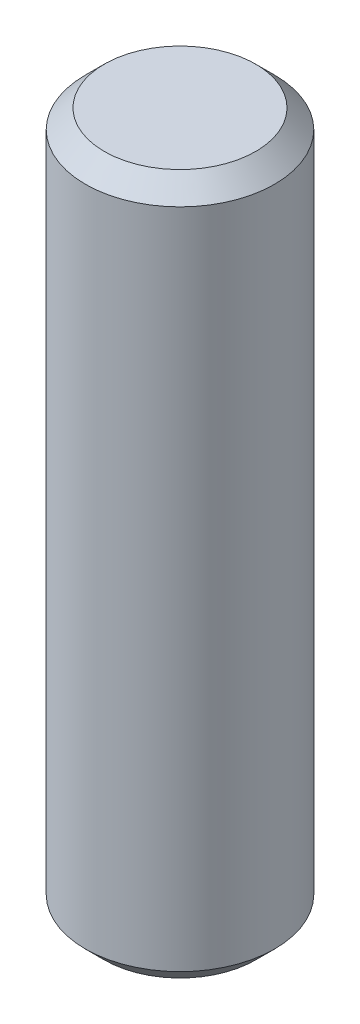
SolidWorks part; units mm, degrees
ref_plane "Front Plane" through (0, 0, 0) normal (0, 0, 1) x (1, 0, 0)
ref_plane "Top Plane" through (0, 0, 0) normal (0, 1, 0) x (1, 0, 0)
ref_plane "Right Plane" through (0, 0, 0) normal (1, 0, 0) x (0, 0, -1)
sketch "Sketch1" plane through (0, 0, 0) normal (0, 1, 0) x (1, 0, 0)
  circle A0 centre (0, 0) radius 10
  dimension "D1" = 20
extrude "Boss-Extrude1" add sketch "Sketch1" along normal mid plane 74
chamfer "Chamfer1" distance 2 angle 45 2 edges at (0, -37, 10) (0, 37, 10)
cosmetic thread "Cosmetic Thread1"
cosmetic thread "Cosmetic Thread2"
